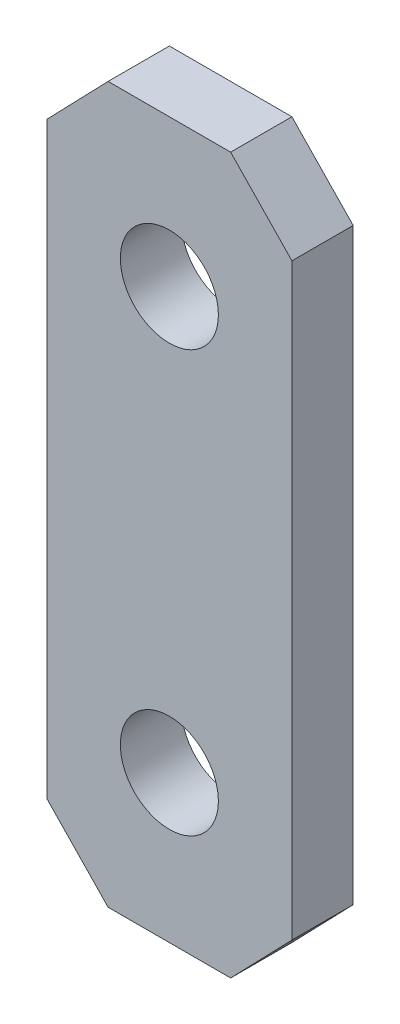
SolidWorks part; units mm, degrees
ref_plane "Front Plane" through (0, 0, 0) normal (0, 0, 1) x (1, 0, 0)
ref_plane "Top Plane" through (0, 0, 0) normal (0, 1, 0) x (1, 0, 0)
ref_plane "Right Plane" through (0, 0, 0) normal (1, 0, 0) x (0, 0, -1)
sketch "Sketch4" plane through (0, 0, 0) normal (0, 0, 1) x (1, 0, 0)
  line L0 (0, 0) -> (12.7, 0)
  line L1 (55, 0) -> (-55, 0) construction
  line L2 (12.7, 0) -> (12.7, 15.24)
  line L3 (12.7, 15.24) -> (9.525, 18.5298)
  line L4 (9.525, 18.5298) -> (3.175, 18.5298)
  line L5 (3.175, 18.5298) -> (0, 15.24)
  line L6 (0, -55) -> (0, 55) construction
  line L7 (0, 15.24) -> (0, 0)
  line L8 (6.35, 0) -> (6.35, 18.5298) construction
  line L9 (0, 15.24) -> (12.7, 15.24) construction
  circle A0 centre (6.35, 10.9098) radius 2.54
  dimension "D5" = 7.62
  dimension "D2" = 5.08
  dimension "D1" = 4.572
  dimension "D3" = 15.24
  dimension "D4" = 12.7
extrude "Boss-Extrude1" add sketch "Sketch4" along normal blind 3.175
mirror "Mirror1" about plane through (0, 0, 0) normal (0, 1, 0) of "Boss-Extrude1"
